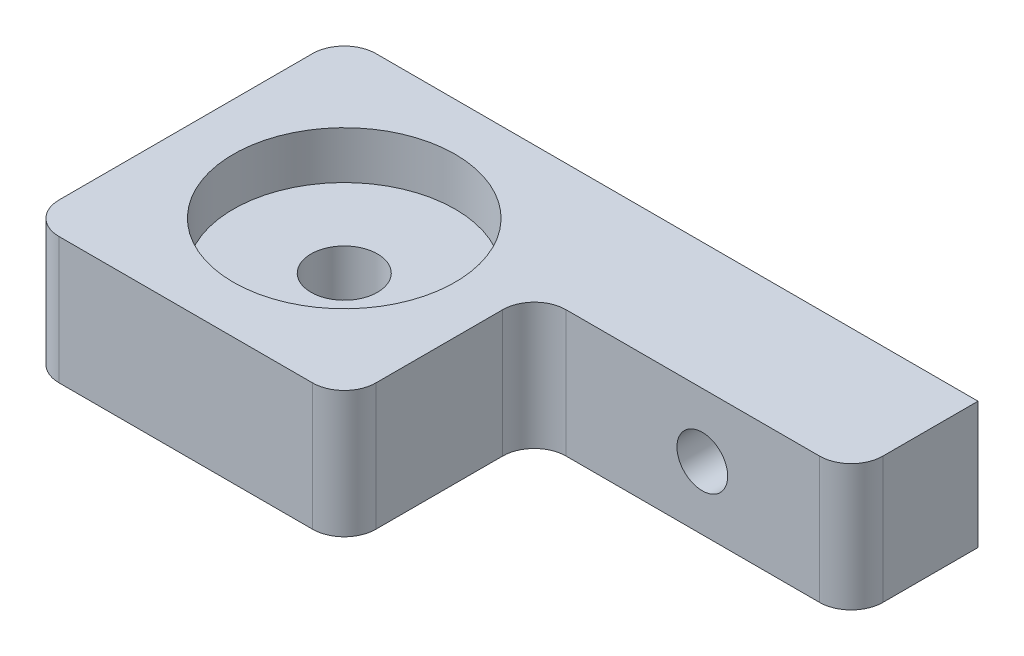
SolidWorks part; units mm, degrees
ref_plane "Plan de face" through (0, 0, 0) normal (0, 0, 1) x (1, 0, 0)
ref_plane "Plan de dessus" through (0, 0, 0) normal (0, 1, 0) x (1, 0, 0)
ref_plane "Plan de droite" through (0, 0, 0) normal (1, 0, 0) x (0, 0, -1)
sketch "Esquisse1" plane through (0, 0, 0) normal (0, 0, 1) x (1, 0, 0)
  line L1 (0, 0) -> (40, 0)
  line L2 (0, 0) -> (0, 8)
  line L3 (0, 8) -> (40, 8)
  line L4 (40, 0) -> (40, 8)
  dimension "D1" = 40
  dimension "D2" = 8
extrude "Boss.-Extru.1" add sketch "Esquisse1" along normal blind 8
sketch "Esquisse2" plane through (0, 0, 8) normal (0, 0, 1) x (1, 0, 0)
  line L0 (0, 0) -> (40, 0) construction
  line L1 (0, 8) -> (20, 8)
  line L2 (0, 8) -> (0, 0)
  line L3 (0, 0) -> (20, 0)
  line L4 (20, 8) -> (20, 0)
  dimension "D1" = 20
extrude "Boss.-Extru.2" add sketch "Esquisse2" along normal blind 12
fillet "Congé1" radius 2 5 edges at (0, 4, 0) (40, 4, 8) (0, 4, 20) (20, 4, 20)
sketch "Esquisse3" plane through (0, 8, 0) normal (0, 1, 0) x (1, 0, 0)
  line L0 (40, 0) -> (2, 0) construction
  line L2 (0, -18) -> (0, -2) construction
  circle A0 centre (10, -10) radius 2.1
  dimension "D1" = 4.2
  dimension "D2" = 10
  dimension "D3" = 10
extrude "Enlèv. mat.-Extru.1" cut sketch "Esquisse3" against normal through all
sketch "Esquisse5" plane through (0, 0, 0) normal (0, 0, -1) x (-1, 0, 0)
  line L0 (0, 8) -> (0, 0) construction
  line L1 (-2, 0) -> (-40, 0) construction
  circle A0 centre (-30.6, 4) radius 1.6
  dimension "D1" = 3.2
  dimension "D2" = 30.6
  dimension "D3" = 4
extrude "Enlèv. mat.-Extru.2" cut sketch "Esquisse5" against normal through all
sketch "Esquisse6" plane through (0, 8, 0) normal (0, 1, 0) x (1, 0, 0)
  circle A0 centre (10, -10) radius 7
  dimension "D1" = 14
extrude "Enlèv. mat.-Extru.3" cut sketch "Esquisse6" against normal blind 3
